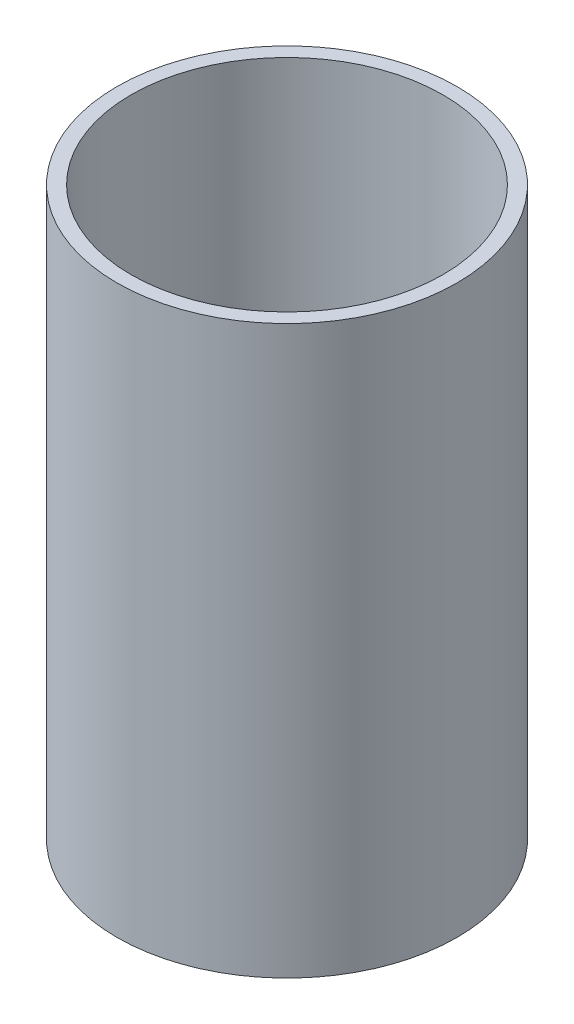
SolidWorks part; units mm, degrees
material "AISI 304"
ref_plane "前视基准面" through (0, 0, 0) normal (0, 0, 1) x (1, 0, 0)
ref_plane "上视基准面" through (0, 0, 0) normal (0, 1, 0) x (1, 0, 0)
ref_plane "右视基准面" through (0, 0, 0) normal (1, 0, 0) x (0, 0, -1)
other "Configuration Table"
sketch "草图1" plane through (0, 0, 0) normal (0, 1, 0) x (1, 0, 0)
  circle A0 centre (0, 0) radius 5.5
  circle A1 centre (0, 0) radius 6
  dimension "D1" = 11
  dimension "D2" = 12
extrude "凸台-拉伸1" add sketch "草图1" along normal blind 20
